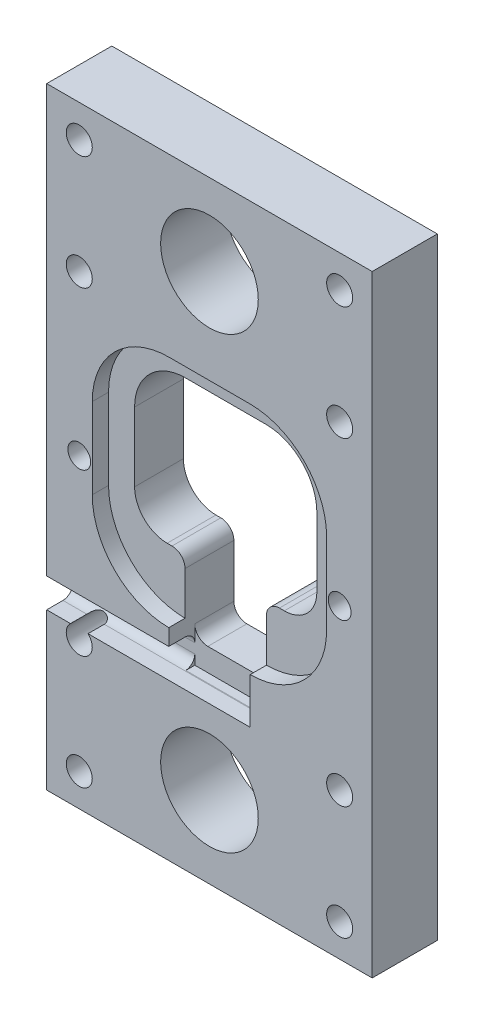
SolidWorks part; units mm, degrees
ref_plane "Front Plane" through (0, 0, 0) normal (0, 0, 1) x (1, 0, 0)
ref_plane "Top Plane" through (0, 0, 0) normal (0, 1, 0) x (1, 0, 0)
ref_plane "Right Plane" through (0, 0, 0) normal (1, 0, 0) x (0, 0, -1)
sketch "Sketch1" plane through (0, 0, 0) normal (0, 0, 1) x (1, 0, 0)
  line L5 (-7, 19) -> (7, 19)
  line L6 (-17, 9) -> (-17, -5)
  line L7 (-7, -15) -> (7, -15)
  line L8 (17, 9) -> (17, -5)
  arc A0 (-7, 19) -> (-17, 9) centre (-7, 9) ccw
  arc A1 (-7, -15) -> (-17, -5) centre (-7, -5) cw
  arc A2 (7, -15) -> (17, -5) centre (7, -5) ccw
  arc A3 (17, 9) -> (7, 19) centre (7, 9) ccw
  point P8 (-17, 19)
  point P11 (-17, -15)
  point P14 (17, -15)
  dimension "D5" = 10
  dimension "D1" = 34
  dimension "D2" = 17
  dimension "D3" = 34
  dimension "D4" = 19
extrude "Boss-Extrude1" add sketch "Sketch1" along normal blind 10
sketch "Sketch2" plane through (0, 0, 0) normal (0, 0, -1) x (-1, 0, 0)
  line L0 (14, 0.39) -> (14, 8.2129)
  line L2 (6.2129, 16) -> (-6.2129, 16)
  line L4 (-14, 8.2129) -> (-14, 0.39)
  line L5 (-14, 0.39) -> (-14, -2.4)
  line L6 (-9, -7.4) -> (-8.25, -7.4)
  line L7 (14, -2.4) -> (14, 0.39)
  line L8 (0, 0) -> (0, 16) construction
  line L10 (6.25, -9.4) -> (6.25, -17.6254)
  line L11 (6.25, -17.6254) -> (-6.25, -17.6254)
  line L12 (-6.25, -9.4) -> (-6.25, -17.6254)
  line L13 (8.25, -7.4) -> (9, -7.4)
  arc A0 (14, 8.2129) -> (6.2129, 16) centre (6.2129, 8.2129) ccw
  arc A1 (-14, 8.2129) -> (-6.2129, 16) centre (-6.2129, 8.2129) cw
  arc A2 (-14, -2.4) -> (-9, -7.4) centre (-9, -2.4) ccw
  arc A3 (14, -2.4) -> (9, -7.4) centre (9, -2.4) cw
  arc A4 (-8.25, -7.4) -> (-6.25, -9.4) centre (-8.25, -9.4) cw
  arc A5 (6.25, -9.4) -> (8.25, -7.4) centre (8.25, -9.4) cw
  point P24 (6.25, -7.4)
  dimension "D3" = 5
  dimension "D4" = 2
  dimension "D1" = 12.5
  dimension "D2" = 6.25
extrude "Cut-Extrude1" cut sketch "Sketch2" against normal through all
sketch "Sketch3" plane through (0, 0, 0) normal (0, 0, -1) x (-1, 0, 0)
  line L0 (0, -0.5076) -> (0, 19) construction
  line L1 (25, -23.0076) -> (-25, -23.0076)
  line L2 (25, -23.0076) -> (25, 21.9924)
  line L3 (25, 21.9924) -> (-25, 21.9924)
  line L4 (-25, -23.0076) -> (-25, 21.9924)
  line L5 (-7, 19) -> (7, 19) construction
  line L6 (0, -0.5076) -> (-19.9583, -0.5076) construction
  line L7 (-6.25, -9.4) -> (-6.25, -15) construction
  line L8 (-9, -7.4) -> (-8.25, -7.4) construction
  line L9 (-14, 8.2129) -> (-14, -2.4) construction
  line L10 (6.2129, 16) -> (-6.2129, 16) construction
  line L11 (14, -2.4) -> (14, 8.2129) construction
  line L12 (8.25, -7.4) -> (9, -7.4) construction
  line L13 (6.25, -9.4) -> (6.25, -15) construction
  line L14 (-6.25, -9.4) -> (-6.25, -15)
  line L15 (-9, -7.4) -> (-8.25, -7.4)
  line L16 (-14, 8.2129) -> (-14, -2.4)
  line L17 (6.2129, 16) -> (-6.2129, 16)
  line L18 (14, -2.4) -> (14, 8.2129)
  line L19 (8.25, -7.4) -> (9, -7.4)
  line L20 (6.25, -9.4) -> (6.25, -15)
  line L21 (6.25, -15) -> (6.25, -17.5)
  line L22 (4.25, -19.5) -> (-4.25, -19.5)
  line L23 (-6.25, -17.5) -> (-6.25, -15)
  arc A0 (-6.25, -9.4) -> (-8.25, -7.4) centre (-8.25, -9.4) ccw construction
  arc A1 (-14, -2.4) -> (-9, -7.4) centre (-9, -2.4) ccw construction
  arc A2 (-6.2129, 16) -> (-14, 8.2129) centre (-6.2129, 8.2129) ccw construction
  arc A3 (14, 8.2129) -> (6.2129, 16) centre (6.2129, 8.2129) ccw construction
  arc A4 (9, -7.4) -> (14, -2.4) centre (9, -2.4) ccw construction
  arc A5 (8.25, -7.4) -> (6.25, -9.4) centre (8.25, -9.4) ccw construction
  arc A6 (-6.25, -9.4) -> (-8.25, -7.4) centre (-8.25, -9.4) ccw
  arc A7 (-14, -2.4) -> (-9, -7.4) centre (-9, -2.4) ccw
  arc A8 (-6.2129, 16) -> (-14, 8.2129) centre (-6.2129, 8.2129) ccw
  arc A9 (14, 8.2129) -> (6.2129, 16) centre (6.2129, 8.2129) ccw
  arc A10 (9, -7.4) -> (14, -2.4) centre (9, -2.4) ccw
  arc A11 (8.25, -7.4) -> (6.25, -9.4) centre (8.25, -9.4) ccw
  arc A12 (-6.25, -17.5) -> (-4.25, -19.5) centre (-4.25, -17.5) ccw
  arc A13 (6.25, -17.5) -> (4.25, -19.5) centre (4.25, -17.5) cw
  dimension "D6" = 2
  dimension "D1" = 45
  dimension "D2" = 50
  dimension "D3" = 25
  dimension "D4" = 22.5
  dimension "D5" = 4.5
extrude "Boss-Extrude3" add sketch "Sketch3" against normal blind 10 contours L2 L1 L4 L3 | L19 A11 L20 L21 A13 L22 A12 L23 L14 A6 L15 A7 L16 A8 L17 A9 L18 A10
sketch "Sketch4" plane through (0, 0, 10) normal (0, 0, 1) x (1, 0, 0)
  line L0 (-25, -23.0076) -> (-25, 21.9924) construction
  line L1 (-18, 8.1924) -> (-18, -4.2076)
  line L2 (25, -23.0076) -> (25, 21.9924) construction
  line L3 (-6.2, -16.0076) -> (6.2, -16.0076)
  line L4 (-25, 21.9924) -> (25, 21.9924) construction
  line L5 (18, -4.2076) -> (18, 8.1924)
  line L6 (-25, -23.0076) -> (25, -23.0076) construction
  line L7 (6.2, 19.9924) -> (-6.2, 19.9924)
  arc A0 (18, 8.1924) -> (6.2, 19.9924) centre (6.2, 8.1924) ccw
  arc A1 (18, -4.2076) -> (6.2, -16.0076) centre (6.2, -4.2076) cw
  arc A2 (-6.2, -16.0076) -> (-18, -4.2076) centre (-6.2, -4.2076) cw
  arc A3 (-18, 8.1924) -> (-6.2, 19.9924) centre (-6.2, 8.1924) cw
  dimension "D5" = 11.8
  dimension "D1" = 7
  dimension "D2" = 7
  dimension "D3" = 2
  dimension "D4" = 7
extrude "Cut-Extrude6" cut sketch "Sketch4" against normal blind 2.5
sketch "Sketch5" plane through (0, 0, 10) normal (0, 0, 1) x (1, 0, 0)
  line L0 (-6.25, -17.5) -> (-6.25, -16.0075) construction
  line L1 (-6.25, -16.7537) -> (6.25, -16.7537)
  line L2 (-6.25, -16.7537) -> (-6.25, -23.0076)
  line L3 (-6.25, -23.0076) -> (6.25, -23.0076)
  line L4 (6.25, -16.7537) -> (6.25, -23.0076)
  line L5 (-25, -23.0076) -> (25, -23.0076) construction
extrude "Cut-Extrude7" cut sketch "Sketch5" against normal blind 4
sketch "Sketch6" plane through (0, 0, 0) normal (0, 0, -1) x (-1, 0, 0)
  line L0 (25, -23.0076) -> (25, 21.9924) construction
  line L1 (25, -23.0076) -> (-25, -23.0076)
  line L2 (25, -23.0076) -> (25, -46.9924)
  line L3 (25, -46.9924) -> (-25, -46.9924)
  line L4 (-25, -23.0076) -> (-25, -46.9924)
  line L5 (25, -23.0076) -> (-25, -23.0076) construction
  line L7 (25, 21.9924) -> (-25, 21.9924)
  line L8 (25, 21.9924) -> (25, 46.9924)
  line L9 (25, 46.9924) -> (-25, 46.9924)
  line L10 (-25, 21.9924) -> (-25, 46.9924)
  circle A0 centre (0, -34.4924) radius 7.5
  circle A1 centre (0, 34.4924) radius 7.5
extrude "Boss-Extrude4" add sketch "Sketch6" against normal up to surface (10 mm away) up to face at (0, -2.2907, 10)
sketch "Sketch7" plane through (-25, 0, 0) normal (-1, 0, 0) x (0, 0, 1)
  line L0 (10, -46.9924) -> (10, 46.9924) construction
  line L1 (10, -18.5124) -> (7.5, -18.5124)
  line L2 (10, -18.5124) -> (10, -23.0124)
  line L3 (10, -23.0124) -> (7.5, -23.0124)
  line L4 (6, -20.0124) -> (6, -21.5124)
  line L6 (10, -46.9924) -> (0, -46.9924) construction
  arc A0 (6, -21.5124) -> (7.5, -23.0124) centre (7.5, -21.5124) ccw
  arc A1 (6, -20.0124) -> (7.5, -18.5124) centre (7.5, -20.0124) cw
  point P10 (6, -23.0124)
  point P13 (6, -18.5124)
  dimension "D4" = 1.5
  dimension "D1" = 23.98
  dimension "D2" = 4.5
  dimension "D3" = 4
extrude "Cut-Extrude8" cut sketch "Sketch7" against normal up to surface (31.25 mm away) up to face at (6.25, -16.4788, 5.875)
sketch "Sketch8" plane through (0, 0, 10) normal (0, 0, 1) x (1, 0, 0)
  circle A0 centre (-20, 41.9924) radius 2
  circle A1 centre (20, 41.9924) radius 2
  circle A2 centre (-20, 0) radius 1.75
  circle A3 centre (20, 0) radius 1.75
  circle A4 centre (20, -41.9924) radius 2
  circle A5 centre (-20, -41.9924) radius 2
  dimension "D1" = 3.5
  dimension "D2" = 3.5
extrude "Cut-Extrude11" cut sketch "Sketch8" against normal through all
sketch "Sketch9" plane through (0, 0, 10) normal (0, 0, 1) x (1, 0, 0)
  circle A0 centre (-20, 24.4924) radius 2
  circle A1 centre (20, 24.4924) radius 2
  circle A2 centre (20, -24.4924) radius 2
  circle A3 centre (-20, -24.4924) radius 2
extrude "Cut-Extrude12" cut sketch "Sketch9" against normal through all
